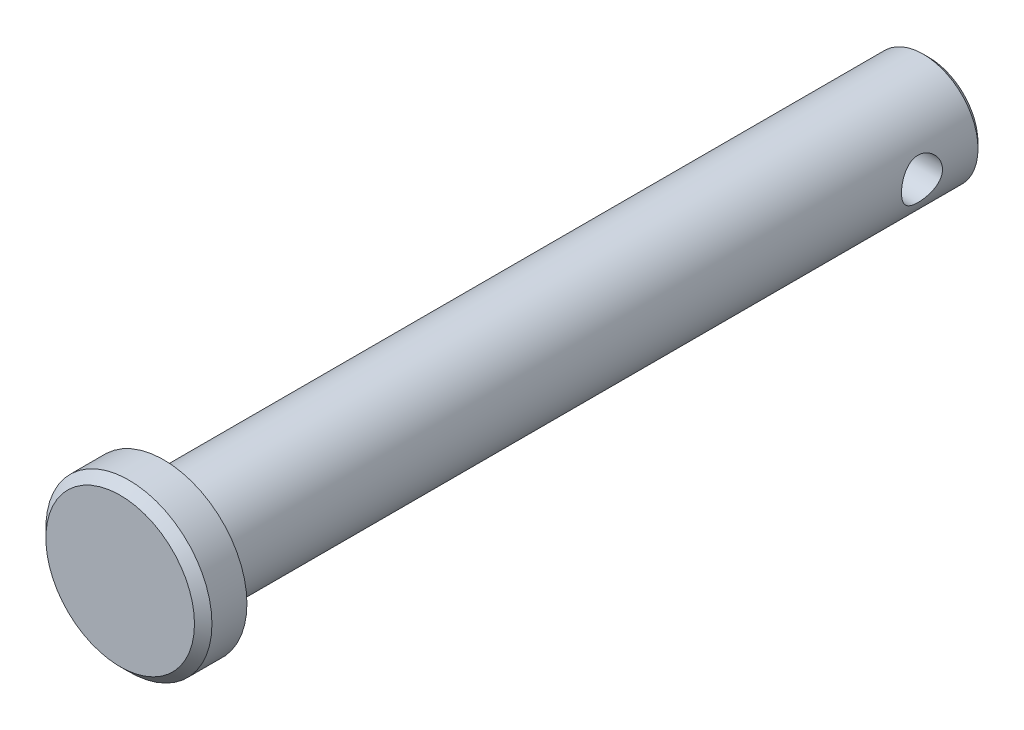
SolidWorks part; units mm, degrees
material "6061 Alloy"
ref_plane "Front" through (0, 0, 0) normal (0, 0, 1) x (1, 0, 0)
ref_plane "Top" through (0, 0, 0) normal (0, 1, 0) x (1, 0, 0)
ref_plane "Right" through (0, 0, 0) normal (1, 0, 0) x (0, 0, -1)
sketch "Sketch1" plane through (0, 0, 0) normal (0, 0, 1) x (1, 0, 0)
  circle A0 centre (0, 0) radius 3.175
  point P3 (0, 3.175)
  point P4 (0, -3.175)
  dimension "dia" = 6.35
extrude "Extrude1" add sketch "Sketch1" along normal mid plane 44.45
sketch "Sketch2" plane through (0, 0, 22.225) normal (0, 0, 1) x (1, 0, 0)
  circle A0 centre (0, 0) radius 4.826
  dimension "head dia" = 9.652
extrude "Extrude2" add sketch "Sketch2" along normal blind 2.54
chamfer "Chamfer1" distance 0.508 angle 45 1 edges at (4.826, 0, 24.765)
sketch "Sketch3" plane through (0, 0, 0) normal (1, 0, 0) x (0, 0, -1)
  line L0 (-22.225, -3.175) -> (-22.225, 3.175) construction
  circle A0 centre (18.6531, 0) radius 1.1906
  point P2 (17.4625, 0)
  dimension "hole dia" = 2.3813
  dimension "useable Lg" = 39.6875
extrude "Extrude3" cut sketch "Sketch3" against normal through all and the other way through all
chamfer "Chamfer2" distance 0.3175 angle 45 1 edges at (3.175, 0, -22.225)
ref_plane "Plane1" through (0, 0, -18.6531) normal (0, 0, 1) x (1, 0, 0)
sketch "Sketch8" plane through (0, 0, 0) normal (1, 0, 0) x (0, 0, -1)
  line L0 (-24.765, 4.318) -> (-24.765, -4.318) construction
  line L1 (-24.257, -4.826) -> (-22.225, -4.826) construction
  line L2 (22.225, -2.8575) -> (22.225, 2.8575) construction
  point P0 (-24.765, 4.826)
  point P1 (-22.225, 4.826)
  point P5 (22.225, 3.175)
  point P8 (-24.765, -4.826)
  point P9 (22.225, -3.175)
equation "\"D1@Chamfer1\" = \"head ht@Extrude2\" * .2"
equation "\"D1@Chamfer2\" = \"dia@Sketch1\" * .05"
